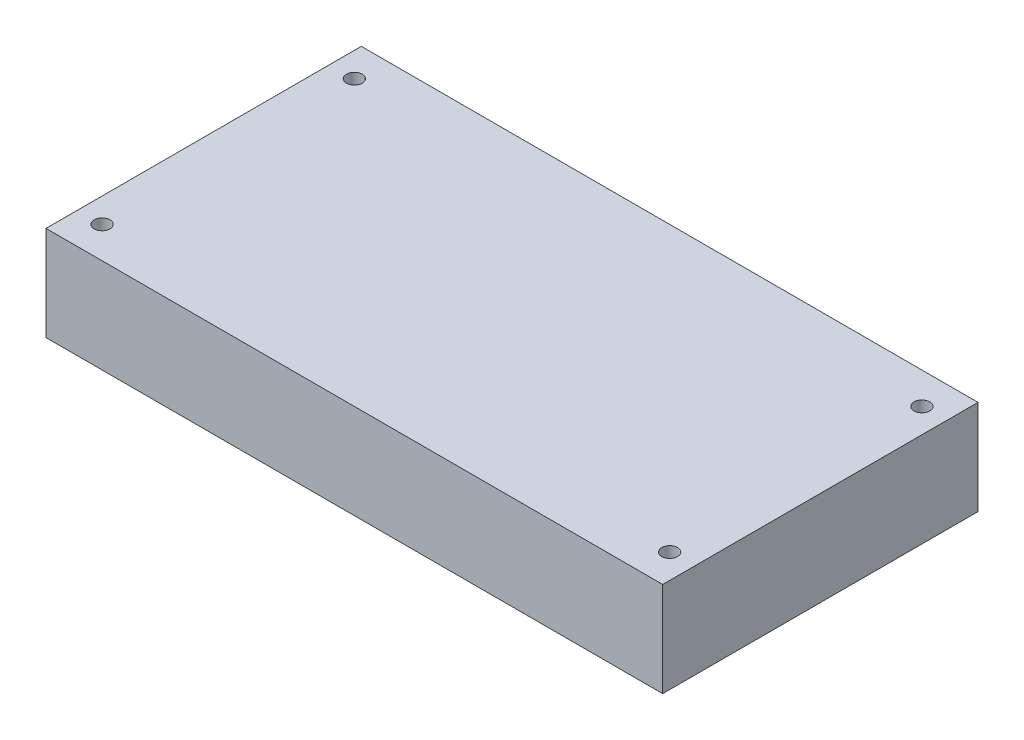
SolidWorks part; units mm, degrees
ref_plane "Front" through (0, 0, 0) normal (0, 0, 1) x (1, 0, 0)
ref_plane "Top" through (0, 0, 0) normal (0, 1, 0) x (1, 0, 0)
ref_plane "Right" through (0, 0, 0) normal (1, 0, 0) x (0, 0, -1)
sketch "Sketch1" plane through (0, 0, 0) normal (0, 1, 0) x (1, 0, 0)
  line L0 (0, 0) -> (-45, 0) construction
  line L1 (-48.895, -25) -> (48.895, -25)
  line L2 (-48.895, -25) -> (-48.895, 25)
  line L3 (-48.895, 25) -> (48.895, 25)
  line L4 (48.895, -25) -> (48.895, 25)
  line L5 (-48.895, -25) -> (48.895, 25) construction
  line L6 (-48.895, 25) -> (48.895, -25) construction
  line L7 (0, 0) -> (45, 0) construction
  line L8 (45, 0) -> (45, 20) construction
  line L9 (-45, 0) -> (-45, 20) construction
  circle A0 centre (45, 20) radius 1.25
  circle A1 centre (-45, 20) radius 1.25
  circle A2 centre (45, -20) radius 1.25
  circle A3 centre (-45, -20) radius 1.25
  point P0 (0, 0)
  dimension "D5" = 2.5
  dimension "D1" = 97.79
  dimension "D2" = 50
  dimension "D3" = 40
  dimension "D4" = 90
  dimension "D6" = 40
extrude "Boss-Extrude1" add sketch "Sketch1" along normal blind 15
